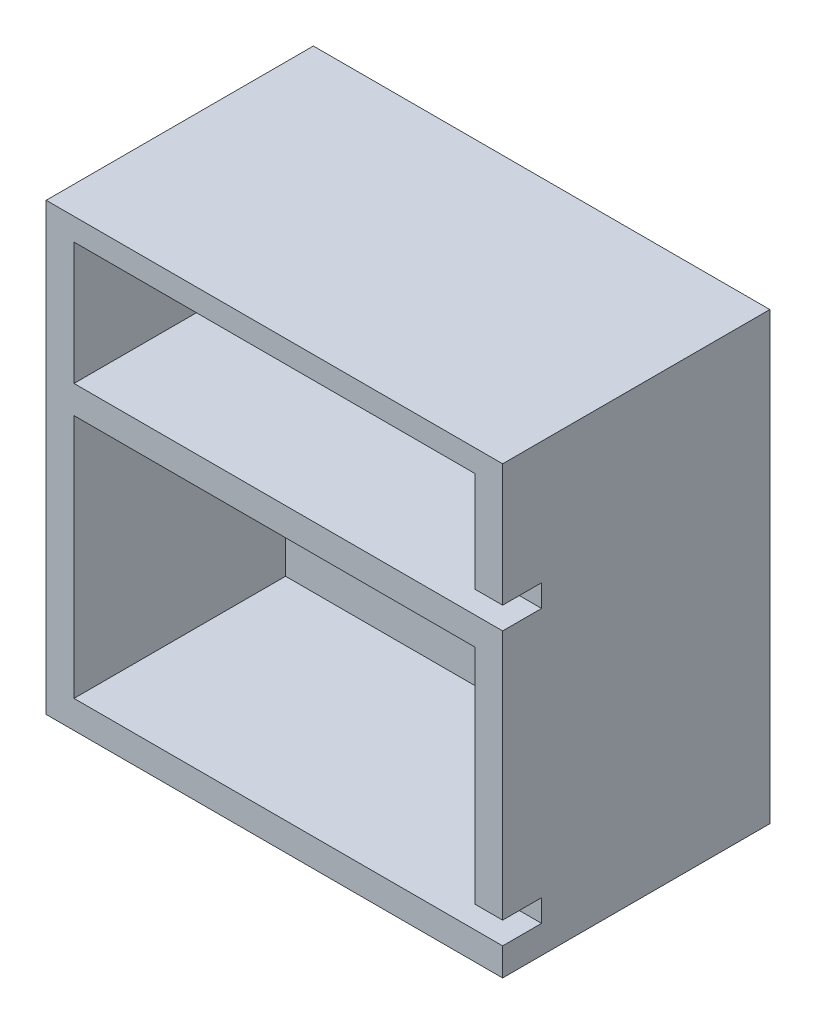
SolidWorks part; units mm, degrees
ref_plane "前基準面" through (0, 0, 0) normal (0, 0, 1) x (1, 0, 0)
ref_plane "上基準面" through (0, 0, 0) normal (0, 1, 0) x (1, 0, 0)
ref_plane "右基準面" through (0, 0, 0) normal (1, 0, 0) x (0, 0, -1)
sketch "草圖1" plane through (0, 0, 0) normal (0, 1, 0) x (1, 0, 0)
  line L1 (-41, 24) -> (41, 24)
  line L2 (-41, 24) -> (-41, -24)
  line L3 (-41, -24) -> (41, -24)
  line L4 (41, 24) -> (41, -24)
  line L5 (-41, 24) -> (41, -24) construction
  line L6 (-41, -24) -> (41, 24) construction
  point P1 (0, 0)
  dimension "D1" = 82
  dimension "D2" = 48
extrude "填料-伸長1" add sketch "草圖1" along normal blind 80
sketch "草圖2" plane through (0, 0, 24) normal (0, 0, 1) x (1, 0, 0)
  line L0 (0, -27.5) -> (0, 27.5) construction
  line L1 (-36, 49) -> (36, 49)
  line L2 (-36, 49) -> (-36, 5)
  line L3 (-36, 5) -> (36, 5)
  line L4 (36, 49) -> (36, 5)
  line L5 (-36, 49) -> (36, 5) construction
  line L6 (-36, 5) -> (36, 49) construction
  line L7 (27.5, 0) -> (-27.5, 0) construction
  line L8 (-36, 76) -> (36, 76)
  line L9 (-36, 76) -> (-36, 54)
  line L10 (-36, 54) -> (36, 54)
  line L11 (36, 76) -> (36, 54)
  line L12 (-36, 76) -> (36, 54) construction
  line L13 (-36, 54) -> (36, 76) construction
  point P0 (0, 27)
  point P7 (0, 65)
  dimension "D1" = 44
  dimension "D2" = 72
  dimension "D3" = 5
  dimension "D4" = 22
  dimension "D5" = 5
extrude "除料-伸長1" cut sketch "草圖2" against normal blind 38
sketch "草圖3" plane through (41, 0, 0) normal (1, 0, 0) x (0, 0, -1)
  line L0 (-24, 80) -> (-24, 0) construction
  line L1 (-17, 9) -> (-24, 9)
  line L2 (-17, 9) -> (-17, 5)
  line L3 (-17, 5) -> (-24, 5)
  line L4 (-24, 9) -> (-24, 5)
  line L5 (-17, 9) -> (-24, 5) construction
  line L6 (-17, 5) -> (-24, 9) construction
  line L7 (14, 54) -> (-24, 54) construction
  line L8 (-17, 58) -> (-24, 58)
  line L9 (-17, 58) -> (-17, 54)
  line L10 (-17, 54) -> (-24, 54)
  line L11 (-24, 58) -> (-24, 54)
  line L12 (-17, 58) -> (-24, 54) construction
  line L13 (-17, 54) -> (-24, 58) construction
  line L14 (14, 5) -> (-24, 5) construction
  point P0 (-20.5, 7)
  point P7 (-20.5, 56)
  dimension "D1" = 4
  dimension "D2" = 7
  dimension "D3" = 4
extrude "除料-伸長2" cut sketch "草圖3" against normal up to next
sketch "草圖5" plane through (0, 0, -14) normal (0, 0, 1) x (1, 0, 0)
  line L0 (-41, 80) -> (-41, 0) construction
  line L1 (-41, 80) -> (41, 80) construction
  circle A0 centre (-21, 60) radius 3.6
  circle A1 centre (15, 60) radius 3.6
  circle A2 centre (15, 24) radius 3.6
  circle A3 centre (-21, 24) radius 3.6
  dimension "D1" = 7.2
  dimension "D2" = 20
  dimension "D3" = 20
  dimension "D4" = 2
  dimension "D5" = 2
extrude "除料-伸長3" cut sketch "草圖5" against normal blind 4.1
sketch "草圖6" plane through (0, 0, -14) normal (0, 0, 1) x (1, 0, 0)
  circle A0 centre (-21, 60) radius 2.25
  circle A1 centre (15, 60) radius 2.25
  circle A2 centre (15, 24) radius 2.25
  circle A3 centre (-21, 24) radius 2.25
  dimension "D1" = 4.5
extrude "除料-伸長4" cut sketch "草圖6" against normal up to next
